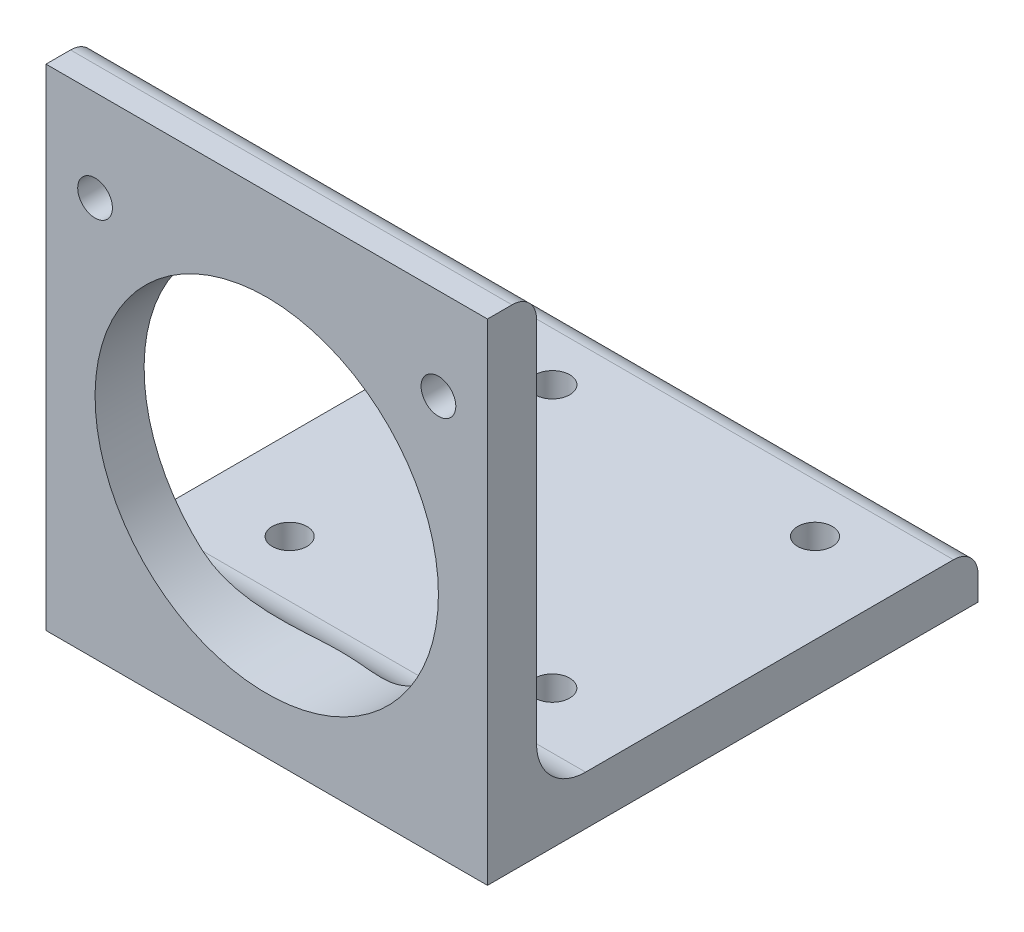
SolidWorks part; units mm, degrees
material "Al 6061-T6"
ref_plane "Front Plane" through (0, 0, 0) normal (0, 0, 1) x (1, 0, 0)
ref_plane "Top Plane" through (0, 0, 0) normal (0, 1, 0) x (1, 0, 0)
ref_plane "Right Plane" through (0, 0, 0) normal (1, 0, 0) x (0, 0, -1)
sketch "Sketch1" plane through (0, 0, 0) normal (1, 0, 0) x (0, 0, -1)
  line L1 (3.175, -31.75) -> (-3.175, -31.75)
  line L2 (3.175, -19.05) -> (3.175, 28.575)
  line L3 (0, 31.75) -> (-3.175, 31.75)
  line L4 (-3.175, -31.75) -> (-3.175, 31.75)
  line L5 (3.175, -31.75) -> (-3.175, 31.75) construction
  line L6 (3.175, 31.75) -> (-3.175, -31.75) construction
  line L7 (-3.175, -31.75) -> (60.325, -31.75)
  line L8 (-3.175, -31.75) -> (-3.175, -25.4)
  line L9 (9.525, -25.4) -> (57.15, -25.4)
  line L10 (60.325, -31.75) -> (60.325, -28.575)
  arc A0 (57.15, -25.4) -> (60.325, -28.575) centre (57.15, -28.575) cw
  arc A1 (3.175, 28.575) -> (0, 31.75) centre (0, 28.575) ccw
  arc A2 (9.525, -25.4) -> (3.175, -19.05) centre (9.525, -19.05) cw
  point P0 (0, 0)
  point P11 (60.325, -25.4)
  dimension "D5" = 3.175
  dimension "D6" = 6.35
  dimension "D1" = 63.5
  dimension "D2" = 63.5
  dimension "D3" = 6.35
  dimension "D4" = 6.35
extrude "Boss-Extrude1" add sketch "Sketch1" along normal blind 57.15 contours L4 L9 L2 L3 | L7 L10 L9 L2 | L9 L4 L1 L2
hole_wizard "M4 Clearance Hole1" positions "Sketch2" profile "Sketch3" hole size "M4" standard "ANSI Metric" end condition through all
sketch "Sketch2" plane through (0, -31.75, 0) normal (0, -1, 0) x (-1, 0, 0)
  line L0 (-28.575, 60.325) -> (-28.575, -3.175) construction
  line L1 (-57.15, 60.325) -> (0, 60.325) construction
  line L2 (-57.15, -3.175) -> (0, -3.175) construction
  point P0 (-45.575, 50.8)
  point P13 (-11.575, 50.8)
  point P14 (-11.575, 16.7894)
  point P15 (-45.575, 16.7894)
  dimension "D1" = 17
  dimension "D2" = 9.525
  dimension "D3" = 2
  dimension "D4" = 2
sketch "Sketch3" plane through (45.575, -31.75, -50.8) normal (1, 0, 0) x (0, 0, -1)
  line L0 (0, 0) -> (0, 63.5)
  line L1 (0, 63.5) -> (2.25, 63.5)
  line L2 (2.25, 63.5) -> (2.25, 0)
  line L5 (2.25, 0) -> (0, 0)
  line L11 (0, -6.35) -> (0, 107.95) construction
  dimension "Thru Hole Dia." = 4.5
  dimension "Thru Hole Depth" = 63.5
sketch "Sketch7" plane through (0, 0, -3.175) normal (0, 0, -1) x (-1, 0, 0)
  line L0 (-28.575, 31.75) -> (-28.575, -25.4) construction
  line L1 (-57.15, 31.75) -> (0, 31.75) construction
  line L2 (-57.15, -25.4) -> (0, -25.4) construction
  line L3 (-57.15, -25.4) -> (0, -25.4) construction
  circle A0 centre (-28.575, -2.3114) radius 22.225
  dimension "D1" = 23.0886
  dimension "D2" = 44.45
extrude "Cut-Extrude1" cut sketch "Sketch7" against normal mid plane 57.15
hole_wizard "#8 Clearance Hole1" positions "Sketch4" profile "Sketch5" hole size "#8" standard "ANSI Inch" end condition through all
sketch "Sketch4" plane through (0, 0, -3.175) normal (0, 0, -1) x (-1, 0, 0)
  line L0 (-28.575, 31.75) -> (-28.575, -25.4) construction
  line L1 (-57.15, 31.75) -> (0, 31.75) construction
  line L2 (-57.15, -25.4) -> (0, -25.4) construction
  circle A0 centre (-28.575, -2.3114) radius 22.225 construction
  circle A1 centre (-28.575, -2.3114) radius 22.225
  point P0 (-50.8, 19.9136)
  point P13 (-6.35, 19.9136)
  dimension "D1" = 22.225
  dimension "D2" = 22.225
  dimension "D3" = 2
sketch "Sketch5" plane through (50.8, 19.9136, -3.175) normal (1, 0, 0) x (0, 1, 0)
  line L0 (0, 0) -> (0, 6.35)
  line L1 (0, 6.35) -> (2.2479, 6.35)
  line L2 (2.2479, 6.35) -> (2.2479, 0)
  line L5 (2.2479, 0) -> (0, 0)
  line L11 (0, -6.35) -> (0, 107.95) construction
  dimension "Thru Hole Dia." = 4.4958
  dimension "Thru Hole Depth" = 6.35
